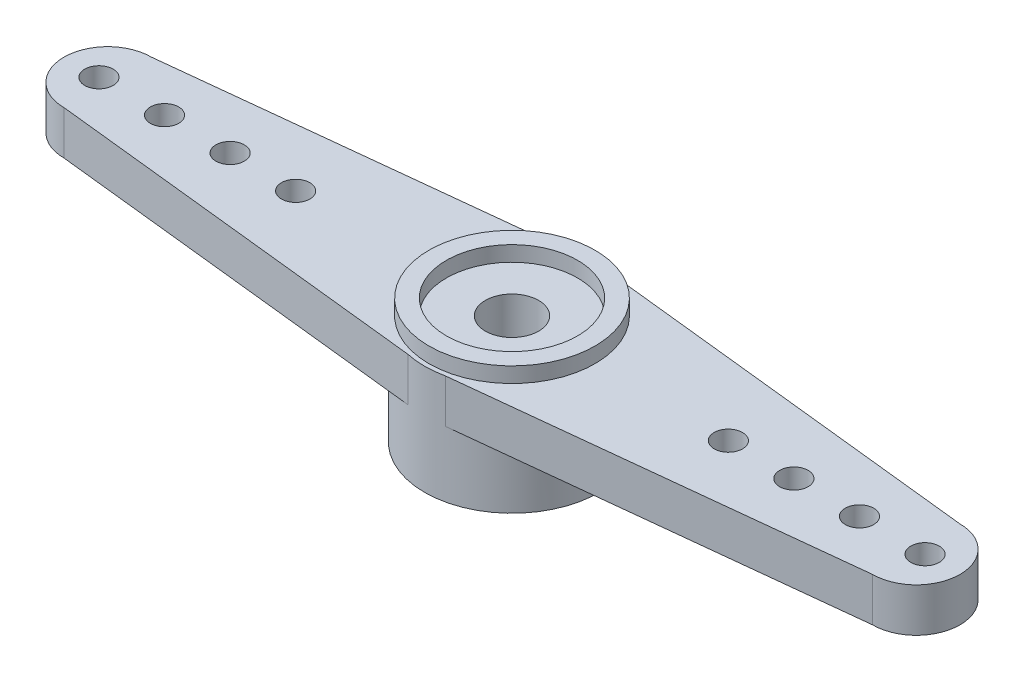
SolidWorks part; units mm, degrees
ref_plane "Front Plane" through (0, 0, 0) normal (0, 0, 1) x (1, 0, 0)
ref_plane "Top Plane" through (0, 0, 0) normal (0, 1, 0) x (1, 0, 0)
ref_plane "Right Plane" through (0, 0, 0) normal (1, 0, 0) x (0, 0, -1)
sketch "Sketch1" plane through (0, 0, 0) normal (0, 1, 0) x (1, 0, 0)
  circle A0 centre (0, 0) radius 4
extrude "Extrude1" add sketch "Sketch1" along normal blind 3
sketch "Sketch2" plane through (0, 3, 0) normal (0, 1, 0) x (1, 0, 0)
  line L3 (-0.8549, 3.9076) -> (-18.5, 2)
  line L4 (-0.8549, -3.9076) -> (-18.5, -2)
  arc A1 (-18.5, 2) -> (-18.5, -2) centre (-18.5, 0) ccw
  arc A2 (-0.8549, -3.9076) -> (-0.8549, 3.9076) centre (0, 0) ccw
extrude "Extrude3" add sketch "Sketch2" along normal blind 2
sketch "Sketch3" plane through (0, 5, 0) normal (0, 1, 0) x (1, 0, 0)
  circle A0 centre (-9.9, 0) radius 0.65
  circle A1 centre (-12.9, 0) radius 0.65
  circle A2 centre (-15.9, 0) radius 0.65
  circle A3 centre (-18.9, 0) radius 0.65
  arc A4 (-18.5, 2) -> (-18.5, -2) centre (-18.5, 0) ccw construction
  dimension "D2" = 1.3
  dimension "D6" = 1.3
  dimension "D7" = 1.3
  dimension "D8" = 1.3
  dimension "D1" = 0.4
  dimension "D3" = 3
  dimension "D4" = 3
  dimension "D5" = 3
extrude "Extrude4" cut sketch "Sketch3" against normal blind 2
sketch "Sketch4" plane through (0, 5, 0) normal (0, 1, 0) x (-1, 0, 0)
  circle A0 centre (0, 0) radius 3.8
extrude "Extrude5" add sketch "Sketch4" along normal blind 0.7
sketch "Sketch5" plane through (0, 5.7, 0) normal (0, 1, 0) x (1, 0, 0)
  circle A0 centre (0, 0) radius 3
extrude "Extrude6" cut sketch "Sketch5" against normal blind 1
sketch "Sketch6" plane through (0, 0, 0) normal (0, -1, 0) x (1, 0, 0)
  circle A0 centre (0, 0) radius 3
extrude "Extrude7" cut sketch "Sketch6" against normal blind 3.7
mirror "Mirror1" about plane through (0, 0, 0) normal (1, 0, 0) of "Extrude4", "Extrude3"
sketch "Sketch7" plane through (0, 5, 0) normal (0, 1, 0) x (1, 0, 0)
  circle A0 centre (0, 0) radius 1.2197
extrude "Extrude8" cut sketch "Sketch7" against normal blind 40
